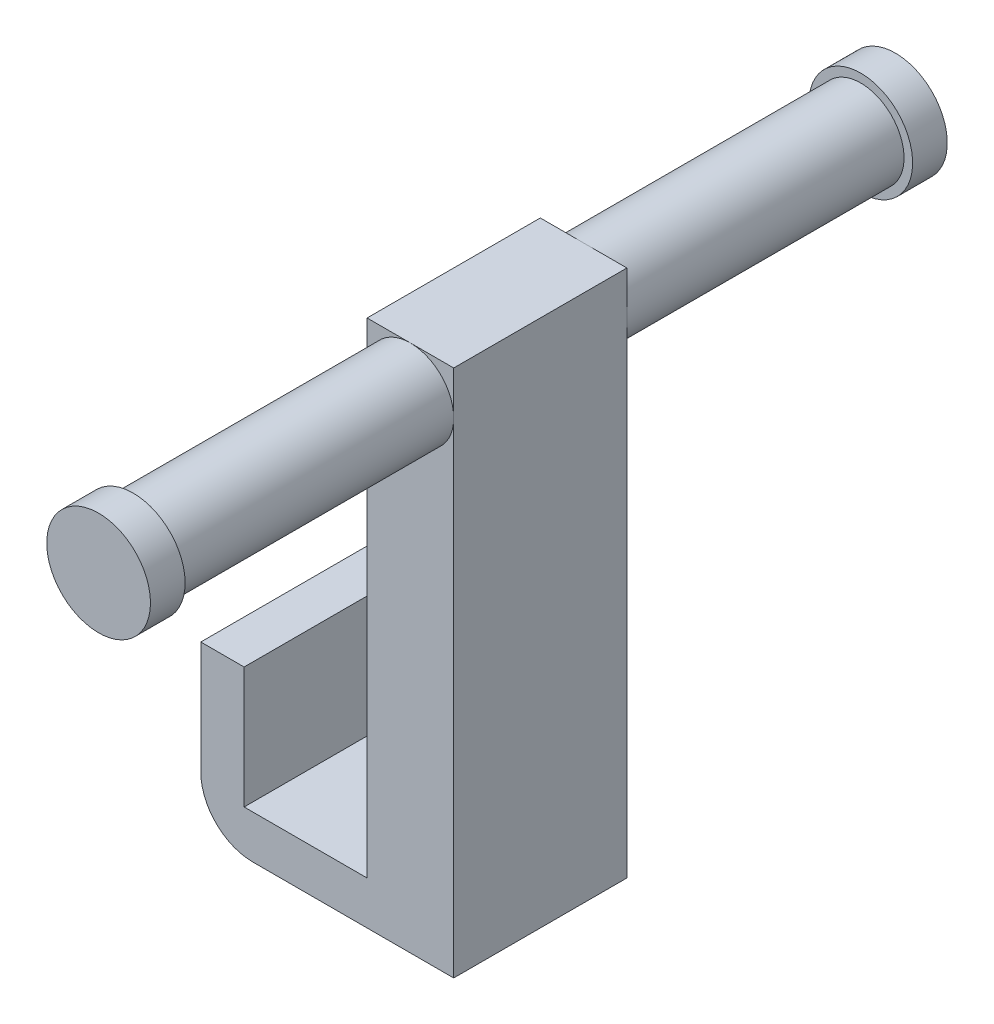
SolidWorks part; units mm, degrees
ref_plane "Front Plane" through (0, 0, 0) normal (0, 0, 1) x (1, 0, 0)
ref_plane "Top Plane" through (0, 0, 0) normal (0, 1, 0) x (1, 0, 0)
ref_plane "Right Plane" through (0, 0, 0) normal (1, 0, 0) x (0, 0, -1)
sketch "Sketch1" plane through (0, 0, 0) normal (1, 0, 0) x (0, 0, -1)
  line L1 (-1.7796, 1.7615) -> (3.2204, 1.7615)
  line L2 (-1.7796, 1.7615) -> (-1.7796, 0.5115)
  line L3 (-1.7796, 0.5115) -> (3.2204, 0.5115)
  line L4 (3.2204, 1.7615) -> (3.2204, 0.5115)
  dimension "D1" = 1.25
  dimension "D2" = 5
extrude "Boss-Extrude1" add sketch "Sketch1" along normal blind 7.3
sketch "Sketch3" plane through (0, 1.7615, 0) normal (0, 1, 0) x (1, 0, 0)
  line L0 (7.3, -1.7796) -> (0, -1.7796) construction
  line L1 (0, 3.2204) -> (1.25, 3.2204)
  line L2 (0, 3.2204) -> (0, -1.7796)
  line L3 (0, -1.7796) -> (1.25, -1.7796)
  line L4 (1.25, 3.2204) -> (1.25, -1.7796)
  dimension "D1" = 1.25
extrude "Boss-Extrude2" add sketch "Sketch3" along normal blind 3.5
sketch "Sketch4" plane through (0, 1.7615, 0) normal (0, 1, 0) x (1, 0, 0)
  line L0 (7.3, -1.7796) -> (1.25, -1.7796) construction
  line L1 (7.3, 3.2204) -> (4.8, 3.2204)
  line L2 (7.3, 3.2204) -> (7.3, -1.7796)
  line L3 (7.3, -1.7796) -> (4.8, -1.7796)
  line L4 (4.8, 3.2204) -> (4.8, -1.7796)
  dimension "D1" = 2.5
extrude "Boss-Extrude3" add sketch "Sketch4" along normal blind 14
sketch "Sketch5" plane through (0, 0, -3.2204) normal (0, 0, -1) x (-1, 0, 0)
  line L0 (-4.8, 15.7615) -> (-4.8, 1.7615) construction
  line L1 (-7.3, 15.7615) -> (-4.8, 15.7615)
  line L2 (-7.3, 15.7615) -> (-7.3, 13.2615)
  line L3 (-7.3, 13.2615) -> (-4.8, 13.2615)
  line L4 (-4.8, 15.7615) -> (-4.8, 13.2615)
  line L5 (-7.3, 15.7615) -> (-4.8, 13.2615)
  circle A0 centre (-6.05, 14.5115) radius 1.25
  dimension "D1" = 2.5
extrude "Boss-Extrude4" add sketch "Sketch5" along normal blind 8 contours A0 L5 | L5 A0
sketch "Sketch6" plane through (0, 0, -11.2204) normal (0, 0, -1) x (-1, 0, 0)
  circle A0 centre (-6.05, 14.5115) radius 1.4971
extrude "Boss-Extrude5" add sketch "Sketch6" along normal blind 1
sketch "Sketch7" plane through (0, 0, 1.7796) normal (0, 0, 1) x (1, 0, 0)
  line L0 (7.3, 15.7615) -> (7.3, 0.5115) construction
  line L1 (4.8, 15.7615) -> (7.3, 15.7615)
  line L2 (4.8, 15.7615) -> (4.8, 9.2664)
  line L3 (4.8, 9.2664) -> (7.3, 9.2664)
  line L4 (7.3, 15.7615) -> (7.3, 9.2664)
  circle A0 centre (6.05, 14.5115) radius 1.25
extrude "Boss-Extrude6" add sketch "Sketch7" along normal blind 8 contours A0 L3
sketch "Sketch8" plane through (0, 0, 9.7796) normal (0, 0, 1) x (1, 0, 0)
  circle A0 centre (6.05, 14.5115) radius 1.4971
extrude "Boss-Extrude7" add sketch "Sketch8" along normal blind 1
fillet "Fillet2" radius 1.5 1 edges at (0, 0.5115, -0.7204)
